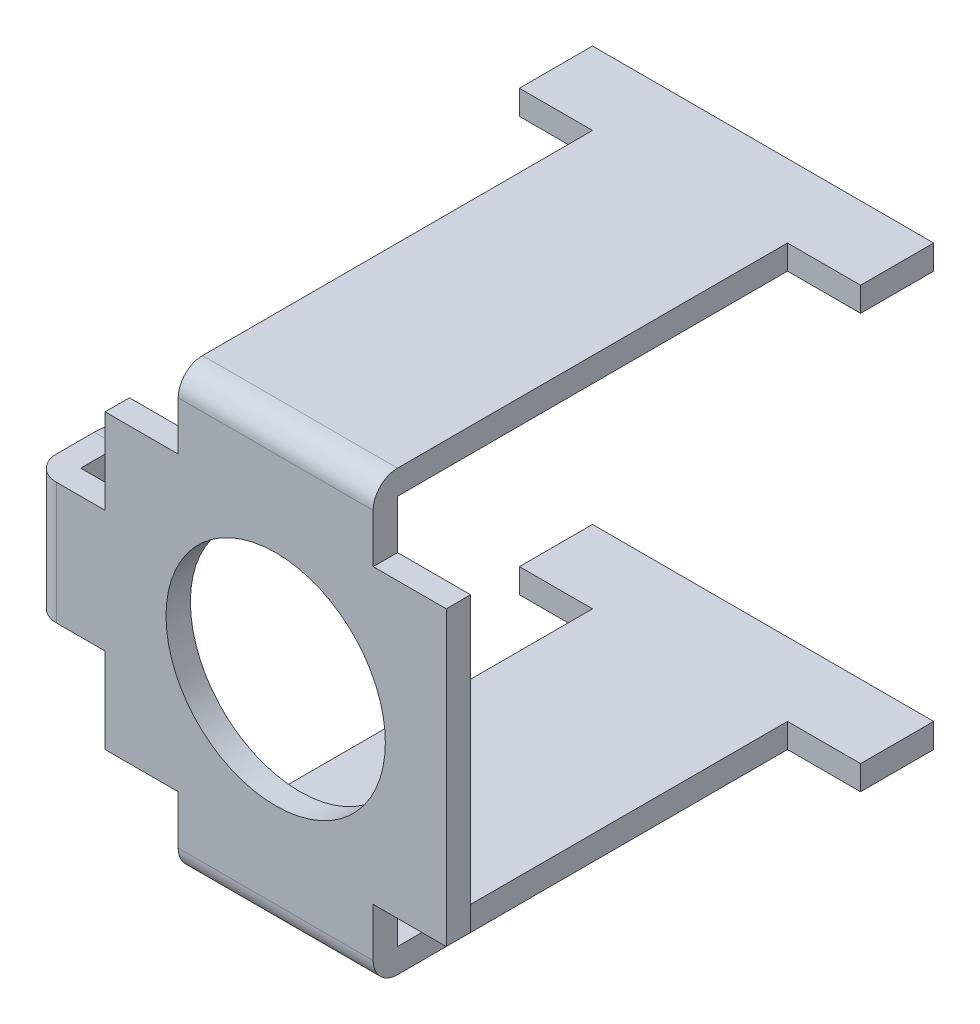
SolidWorks part; units mm, degrees
material "Plain Carbon Steel"
ref_plane "Front Plane" through (0, 0, 0) normal (0, 0, 1) x (1, 0, 0)
ref_plane "Top Plane" through (0, 0, 0) normal (0, 1, 0) x (1, 0, 0)
ref_plane "Right Plane" through (0, 0, 0) normal (1, 0, 0) x (0, 0, -1)
sketch "Sketch1" plane through (0, 0, 0) normal (0, 0, 1) x (1, 0, 0)
  line L32 (4, 6) -> (4, 8)
  line L33 (4, 8) -> (-4, 8)
  line L34 (-4, 8) -> (-4, 6)
  line L35 (-4, 6) -> (-7, 6)
  line L36 (-7, 6) -> (-7, 2.5)
  line L37 (-7, 2.5) -> (-9, 2.5)
  line L38 (-9, 2.5) -> (-9, -2.5)
  line L39 (-9, -2.5) -> (-7, -2.5)
  line L40 (-7, -2.5) -> (-7, -6)
  line L41 (-7, -6) -> (-4, -6)
  line L42 (-4, -6) -> (-4, -8)
  line L43 (-4, -8) -> (4, -8)
  line L44 (4, -8) -> (4, -6)
  line L45 (4, -6) -> (7, -6)
  line L46 (7, -6) -> (7, 6)
  line L47 (7, 6) -> (4, 6)
  circle A1 centre (0, 0) radius 4.5
extrude "Boss-Extrude1" add sketch "Sketch1" along normal blind 1
sketch "Sketch2" plane through (-9, 0, 0) normal (-1, 0, 0) x (0, 0, 1)
  line L0 (1, -2.5) -> (0, -2.5) construction
  line L1 (1, 2.5) -> (-1.55, 2.5)
  line L2 (1, 2.5) -> (1, -2.5)
  line L3 (1, -2.5) -> (-1.55, -2.5)
  line L4 (-4, 0.05) -> (-4, -0.05)
  arc A0 (-4, -0.05) -> (-1.55, -2.5) centre (-1.55, -0.05) ccw
  arc A1 (-4, 0.05) -> (-1.55, 2.5) centre (-1.55, 0.05) cw
  circle A2 centre (-1.55, -0.05) radius 0.5
  point P11 (-4, 2.5)
  dimension "D2" = 2.45
  dimension "D3" = 1
  dimension "D1" = 5
extrude "Boss-Extrude2" add sketch "Sketch2" along normal blind 1
sketch "Sketch3" plane through (0, 8, 0) normal (0, 1, 0) x (1, 0, 0)
  line L17 (4, 0) -> (4, 16)
  line L18 (4, 16) -> (7, 16)
  line L19 (7, 16) -> (7, 19)
  line L20 (7, 19) -> (-7, 19)
  line L21 (-7, 19) -> (-7, 16)
  line L22 (-7, 16) -> (-4, 16)
  line L23 (-4, 16) -> (-4, 0)
  line L25 (-4, 0) -> (-4, -1)
  line L26 (-4, -1) -> (4, -1)
  line L27 (4, -1) -> (4, 0)
extrude "Boss-Extrude3" add sketch "Sketch3" along normal blind 1
sketch "Sketch4" plane through (0, -8, 0) normal (0, -1, 0) x (1, 0, 0)
  line L8 (-4, 1) -> (-4, -16)
  line L9 (4, 1) -> (-4, 1)
  line L10 (4, -16) -> (4, 1)
  line L11 (7, -16) -> (4, -16)
  line L12 (7, -19) -> (7, -16)
  line L13 (-7, -19) -> (7, -19)
  line L14 (-7, -16) -> (-7, -19)
  line L15 (-4, -16) -> (-7, -16)
  line L16 (-4, 1) -> (-4, -16)
  line L17 (4, 1) -> (-4, 1)
  line L18 (4, -16) -> (4, 1)
  line L19 (7, -16) -> (4, -16)
  line L20 (7, -19) -> (7, -16)
  line L21 (-7, -19) -> (7, -19)
  line L22 (-7, -16) -> (-7, -19)
  line L23 (-4, -16) -> (-7, -16)
  dimension "D1" = 0
extrude "Boss-Extrude4" add sketch "Sketch4" along normal blind 1
fillet "Fillet1" radius 1 3 edges at (-10, 0, 1) (0, 9, 1) (0, -9, 1)
